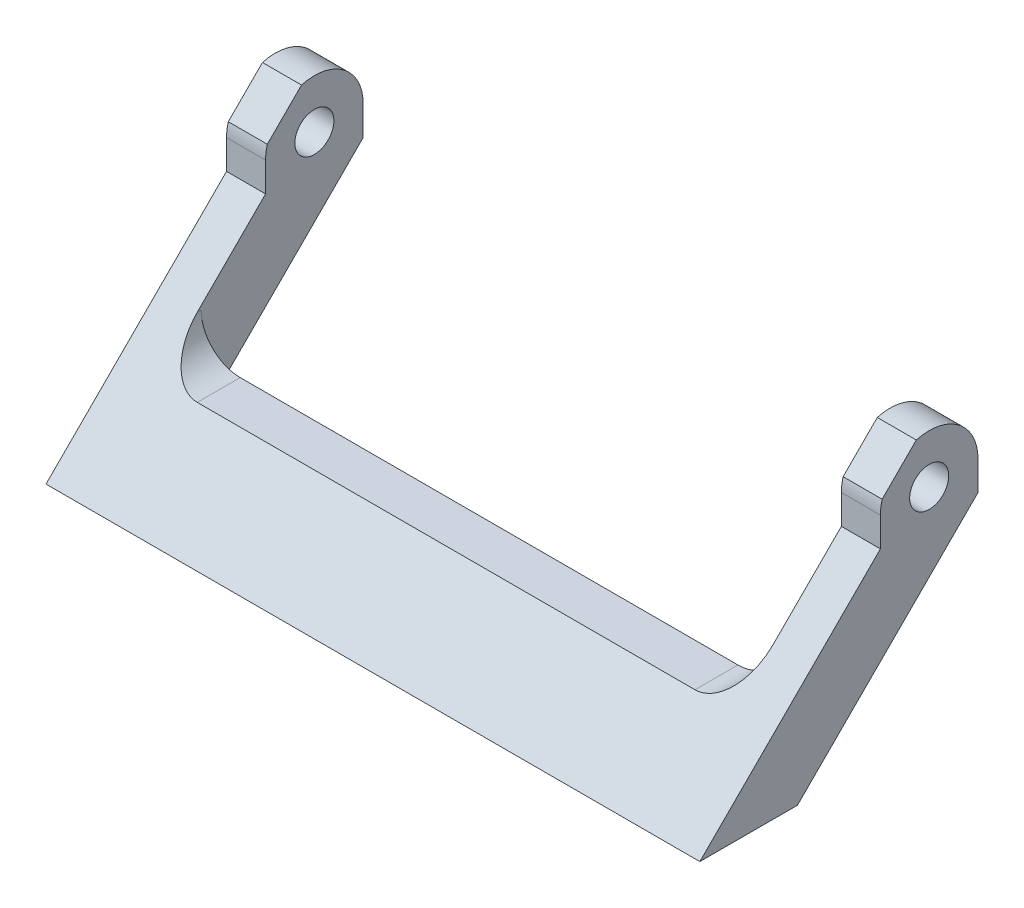
SolidWorks part; units mm, degrees
ref_plane "Front Plane" through (0, 0, 0) normal (0, 0, 1) x (1, 0, 0)
ref_plane "Top Plane" through (0, 0, 0) normal (0, 1, 0) x (1, 0, 0)
ref_plane "Right Plane" through (0, 0, 0) normal (1, 0, 0) x (0, 0, -1)
sketch "Sketch1" plane through (0, 0, 0) normal (1, 0, 0) x (0, 0, -1)
  line L0 (11.9, 1.9) -> (11.9, 0)
  line L1 (11.9, 0) -> (0, 0)
  line L2 (0, 0) -> (18.5, 18.5)
  line L3 (18.5, 18.5) -> (18.5, 21.5)
  line L4 (28.5, 21.5) -> (28.5, 18.5)
  line L5 (28.5, 18.5) -> (11.9, 1.9)
  arc A0 (18.5, 21.5) -> (28.5, 21.5) centre (23.5, 21.5) cw
  circle A1 centre (23.5, 21.5) radius 2
  dimension "D6" = 4
  dimension "D1" = 11.9
  dimension "D2" = 45
  dimension "D3" = 10
  dimension "D4" = 1.9
  dimension "D5" = 18.5
  dimension "D7" = 21.5
extrude "Boss-Extrude1" add sketch "Sketch1" along normal blind 67
sketch "Sketch2" plane through (0, 0, -28.5) normal (0, 0, -1) x (-1, 0, 0)
  line L0 (-63, 26.5) -> (-63, 11.5)
  line L1 (0, 26.5) -> (-67, 26.5) construction
  line L2 (-59, 7.5) -> (-8, 7.5)
  line L3 (-4, 11.5) -> (-4, 26.5)
  line L4 (-4, 26.5) -> (-63, 26.5)
  line L5 (-67, 1.9) -> (-67, 18.5) construction
  line L6 (0, 21.5) -> (0, 26.5) construction
  line L7 (-67, 0) -> (0, 0) construction
  arc A0 (-8, 7.5) -> (-4, 11.5) centre (-8, 11.5) ccw
  arc A1 (-63, 11.5) -> (-59, 7.5) centre (-59, 11.5) ccw
  dimension "D4" = 4
  dimension "D1" = 4
  dimension "D2" = 4
  dimension "D3" = 7.5
extrude "Cut-Extrude1" cut sketch "Sketch2" against normal up to next
sketch "Sketch3" plane through (0, 0, 0) normal (0, -1, 0) x (1, 0, 0)
  line L0 (4, -21.5) -> (63, -21.5)
  line L1 (4, -21.5) -> (4, -11.9)
  line L2 (63, -21.5) -> (63, -11.9)
  line L3 (4, -11.9) -> (63, -11.9)
  line L4 (67, -11.9) -> (0, -11.9) construction
extrude "Cut-Extrude2" cut sketch "Sketch3" against normal up to next
sketch "Sketch4" plane through (67, 0, 0) normal (1, 0, 0) x (0, 0, -1)
  line L0 (26.3966, 30.5388) -> (-4.3198, -0.1777)
  line L1 (26.3966, 30.5388) -> (33.4677, 23.4677)
  line L2 (-4.3198, -0.1777) -> (2.7513, -7.2487)
  line L3 (33.4677, 23.4677) -> (2.7513, -7.2487)
  line L4 (26.3966, 30.5388) -> (2.7513, -7.2487) construction
  line L5 (-4.3198, -0.1777) -> (33.4677, 23.4677) construction
  line L6 (11.9, 1.9) -> (28.5, 18.5) construction
  arc A0 (28.5, 21.5) -> (18.5, 21.5) centre (23.5, 21.5) ccw construction
  point P1 (14.574, 11.645)
  dimension "D2" = 10
  dimension "D3" = 10
  dimension "D4" = 35
extrude "Cut-Extrude3" cut sketch "Sketch4" against normal through all flip side to cut
